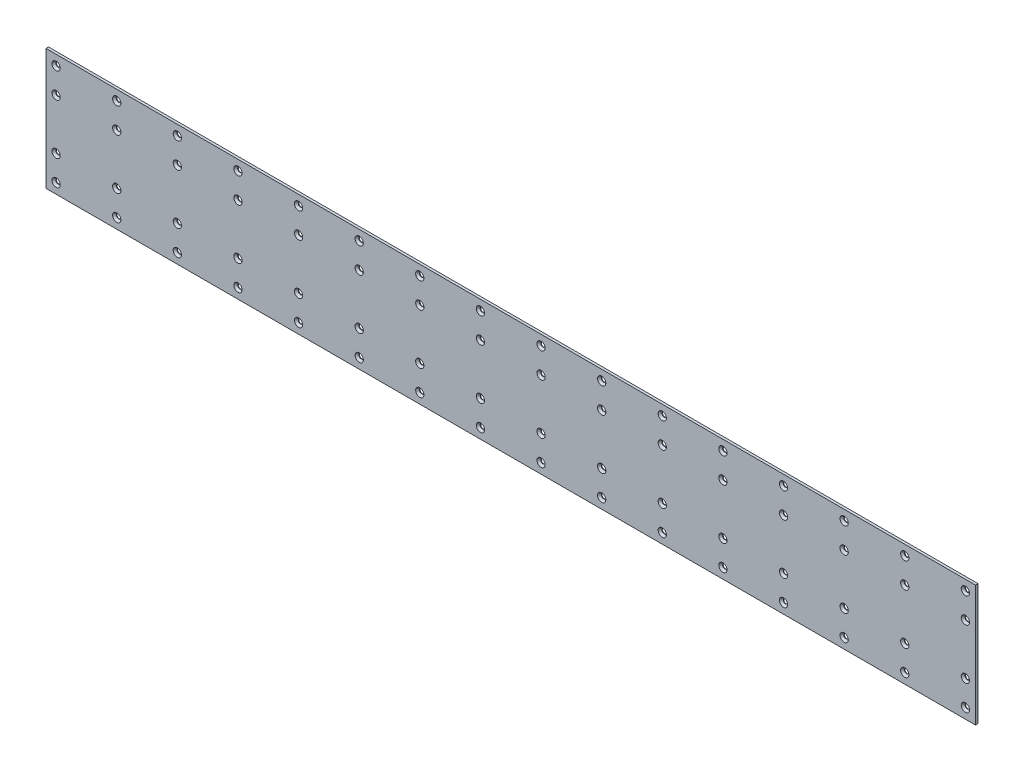
SolidWorks part; units mm, degrees
material "1060 Alloy"
ref_plane "Front Plane" through (0, 0, 0) normal (0, 0, 1) x (1, 0, 0)
ref_plane "Top Plane" through (0, 0, 0) normal (0, 1, 0) x (1, 0, 0)
ref_plane "Right Plane" through (0, 0, 0) normal (1, 0, 0) x (0, 0, -1)
sketch "Sketch1" plane through (0, 0, 0) normal (0, 0, 1) x (1, 0, 0)
  line L1 (0, 0) -> (1168.4, 0)
  line L2 (0, 0) -> (0, 152.4)
  line L3 (0, 152.4) -> (1168.4, 152.4)
  line L4 (1168.4, 0) -> (1168.4, 152.4)
  dimension "D1" = 1168.4
  dimension "D2" = 152.4
extrude "Boss-Extrude1" add sketch "Sketch1" against normal blind 3.175
sketch "Sketch2" plane through (0, 0, 0) normal (0, 0, 1) x (1, 0, 0)
  line L0 (12.7, 139.7) -> (1155.7, 139.7) construction
  line L1 (12.7, 107.95) -> (1155.7, 107.95) construction
  line L2 (12.7, 44.45) -> (1155.7, 44.45) construction
  line L3 (12.7, 12.7) -> (1155.7, 12.7) construction
  line L4 (0, 152.4) -> (0, 0) construction
  line L5 (1168.4, 152.4) -> (0, 152.4) construction
  line L6 (0, 0) -> (1168.4, 0) construction
  dimension "D1" = 12.7
  dimension "D2" = 12.7
  dimension "D3" = 12.7
  dimension "D4" = 31.75
  dimension "D5" = 31.75
  dimension "D6" = 1143
hole_wizard "CSK for #0 Flat Head Machine Screw (100)1" positions "3DSketch1" profile "Sketch3" countersink size "#0" standard "ANSI Inch" end condition through all
sketch3d "3DSketch1"
  point P0 (12.7, 139.7, 0)
  point P3 (12.7, 107.95, 0)
  point P6 (12.7, 44.45, 0)
  point P9 (12.7, 12.7, 0)
sketch "Sketch3" plane through (12.7, 139.7, 0) normal (1, 0, 0) x (0, -1, 0)
  line L0 (0, 0) -> (0, 3.175)
  line L1 (0, 3.175) -> (2.7559, 3.175)
  line L2 (2.7559, 3.175) -> (2.7559, 2.4384)
  line L3 (2.7559, 2.4384) -> (5.1943, 0)
  line L5 (5.1943, 0) -> (0, 0)
  line L6 (-2.7559, 2.4384) -> (-5.1943, 0) construction
  line L11 (0, -6.35) -> (0, 107.95) construction
  dimension "Thru Hole Dia." = 5.5118
  dimension "Thru Hole Depth" = 3.175
  dimension "Near C'Sink Dia." = 10.3886
  dimension "Near C'Sink Angle" = 90
pattern_linear "LPattern1" count 16 spacing 76.2 along (1, 0, 0) of "CSK for #0 Flat Head Machine Screw (100)1"
